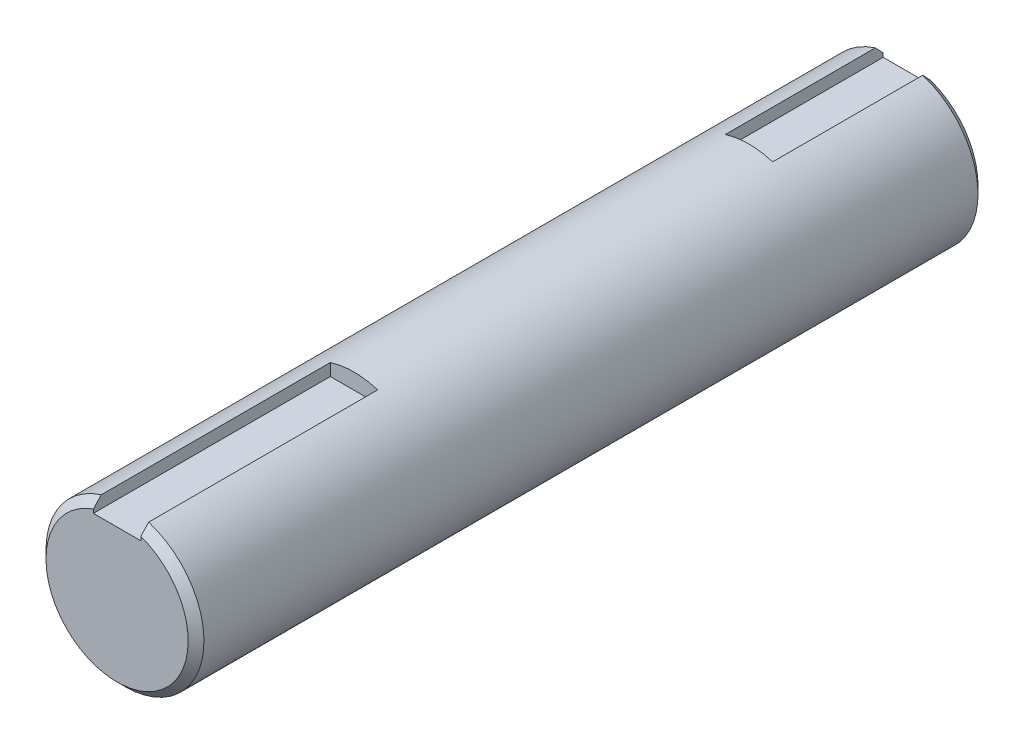
SolidWorks part; units mm, degrees
ref_plane "Front Plane" through (0, 0, 0) normal (0, 0, 1) x (1, 0, 0)
ref_plane "Top Plane" through (0, 0, 0) normal (0, 1, 0) x (1, 0, 0)
ref_plane "Right Plane" through (0, 0, 0) normal (1, 0, 0) x (0, 0, -1)
sketch "Sketch1" plane through (0, 0, 0) normal (0, 0, 1) x (1, 0, 0)
  circle A0 centre (0, 0) radius 10
  dimension "D1" = 20
extrude "Boss-Extrude1" add sketch "Sketch1" along normal blind 100
sketch "Sketch2" plane through (0, 0, 100) normal (0, 0, 1) x (1, 0, 0)
  line L1 (-3, 10.8501) -> (3, 10.8501)
  line L2 (-3, 10.8501) -> (-3, 8)
  line L3 (-3, 8) -> (3, 8)
  line L4 (3, 10.8501) -> (3, 8)
  circle A0 centre (0, 0) radius 10 construction
  point P4 (0, 8)
  dimension "D1" = 6
  dimension "D2" = 8
extrude "Cut-Extrude1" cut sketch "Sketch2" against normal blind 30
sketch "Sketch3" plane through (0, 0, 0) normal (0, 0, -1) x (-1, 0, 0)
  line L1 (-3, 10.6609) -> (3, 10.6609)
  line L2 (-3, 10.6609) -> (-3, 8)
  line L3 (-3, 8) -> (3, 8)
  line L4 (3, 10.6609) -> (3, 8)
  point P4 (0, 8)
  dimension "D1" = 6
  dimension "D2" = 8
extrude "Cut-Extrude2" cut sketch "Sketch3" against normal blind 20
chamfer "Chamfer1" distance 1 angle 45 2 edges at (0, -10, 0) (0, -10, 100)
